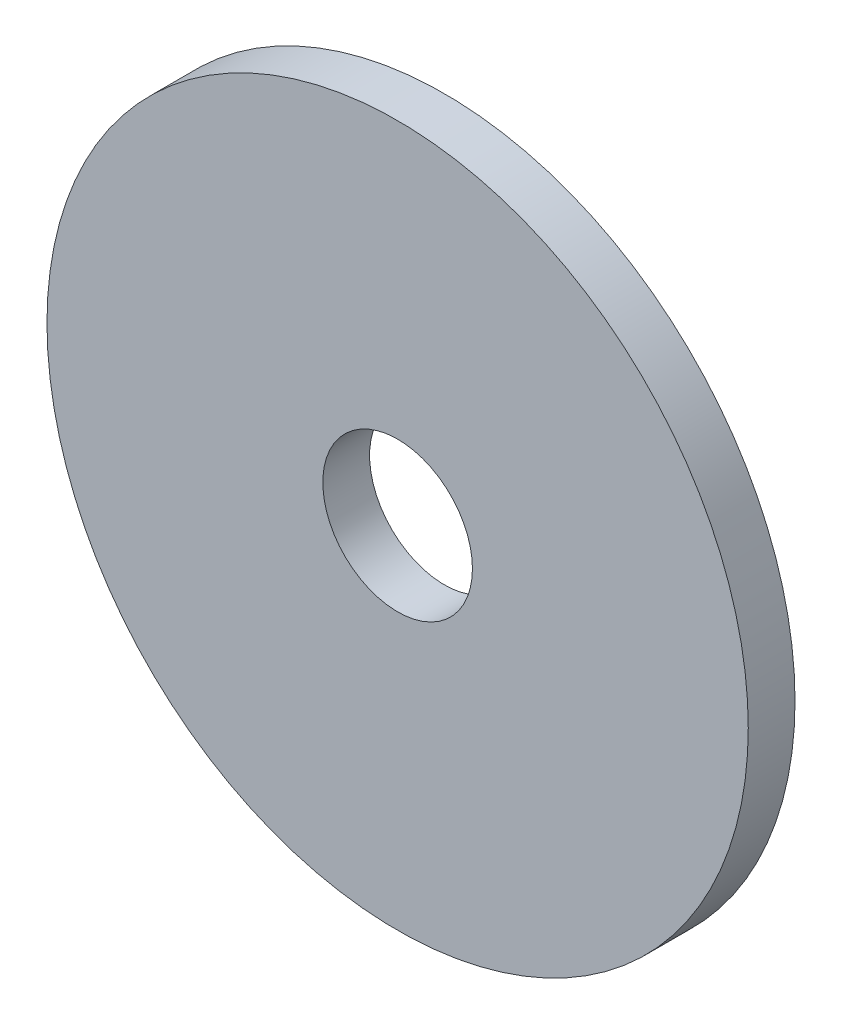
SolidWorks part; units mm, degrees
material "1060 Alloy"
ref_plane "Front Plane" through (0, 0, 0) normal (0, 0, 1) x (1, 0, 0)
ref_plane "Top Plane" through (0, 0, 0) normal (0, 1, 0) x (1, 0, 0)
ref_plane "Right Plane" through (0, 0, 0) normal (1, 0, 0) x (0, 0, -1)
sketch "Sketch1" plane through (0, 0, 0) normal (0, 0, 1) x (1, 0, 0)
  circle A0 centre (0, 0) radius 7.5
  dimension "D1" = 15
extrude "Boss-Extrude1" add sketch "Sketch1" along normal blind 1
hole_wizard "M3 Clearance Hole1" positions "Sketch2" profile "Sketch3" hole size "M3" standard "ANSI Metric"
sketch "Sketch2" plane through (0, 0, 1) normal (0, 0, 1) x (1, 0, 0)
  point P0 (0, 0)
sketch "Sketch3" plane through (0, 0, 1) normal (1, 0, 0) x (0, -1, 0)
  line L0 (0, 0) -> (0, 10.9614)
  line L1 (0, 10.9614) -> (1.6, 10)
  line L2 (1.6, 10) -> (1.6, 0)
  line L5 (1.6, 0) -> (0, 0)
  line L10 (0, 10.9614) -> (-1.6, 10) construction
  line L11 (0, -6.35) -> (0, 107.95) construction
  dimension "Hole Dia." = 3.2
  dimension "Hole Depth" = 10
  dimension "Drill Angle" = 118
equation "\"tubeOutDiameter\" = 35mm"
equation "\"wheelShaftDiameter\"= 12mm"
equation "\"wheelThickness\"= 135mm"
equation "\"BearingDiameter\"= 20mm"
equation "\"BearingThickness\"= 10mm"
equation "\"frontShaftDiameter\"= 20mm"
equation "\"D1@Sketch1\"=\"wheelShaftDiameter\"+3mm"
